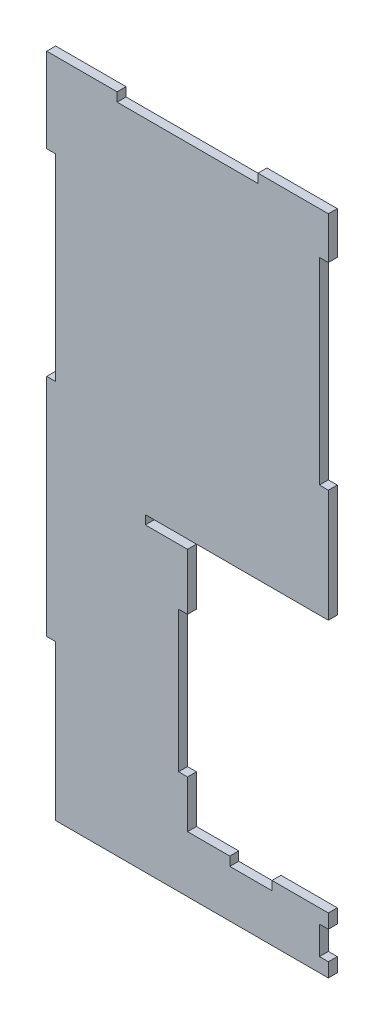
SolidWorks part; units mm, degrees
ref_plane "Front Plane" through (0, 0, 0) normal (0, 0, 1) x (1, 0, 0)
ref_plane "Top Plane" through (0, 0, 0) normal (0, 1, 0) x (1, 0, 0)
ref_plane "Right Plane" through (0, 0, 0) normal (1, 0, 0) x (0, 0, -1)
sketch "Sketch1" plane through (0, 0, 0) normal (0, 0, 1) x (1, 0, 0)
  line L0 (-186.7725, 0) -> (178.836, 0) construction
  line L1 (0, 287.0857) -> (0, -126.9841) construction
  line L2 (100, 287.0857) -> (100, -117.9894) construction
  line L3 (-179.3651, 235) -> (228.5714, 235) construction
  line L4 (-9.3722, 220) -> (110.0222, 220) construction
  line L5 (3.175, 0) -> (3.175, 55)
  line L6 (3.175, 55) -> (0, 55)
  line L7 (0, 55) -> (0, 135)
  line L8 (0, 135) -> (3.175, 135)
  line L9 (3.175, 135) -> (3.175, 205)
  line L10 (3.175, 205) -> (0, 205)
  line L11 (0, 205) -> (0, 235)
  line L12 (0, 235) -> (100, 235)
  line L13 (100, 235) -> (100, 220)
  line L14 (100, 110) -> (50, 110)
  line L15 (50, 106.825) -> (50, 86.825)
  line L16 (50, 20) -> (100, 20)
  line L17 (100, 20) -> (100, 0)
  line L18 (100, 0) -> (3.175, 0)
  line L19 (100, 220) -> (96.825, 220)
  line L20 (96.825, 220) -> (96.825, 150)
  line L21 (96.825, 150) -> (100, 150)
  line L22 (100, 150) -> (100, 110)
  line L23 (50, 110) -> (35, 110)
  line L24 (35, 110) -> (35, 106.825)
  line L25 (35, 106.825) -> (50, 106.825)
  line L26 (72.7222, 86.825) -> (-38.8167, 86.825) construction
  line L27 (50, 86.825) -> (46.825, 86.825)
  line L28 (46.825, 86.825) -> (46.825, 36.825)
  line L29 (46.825, 36.825) -> (50, 36.825)
  line L30 (50, 36.825) -> (50, 20)
  line L32 (46.825, 20) -> (115.3757, 20) construction
  dimension "D1" = 100
  dimension "D2" = 235
  dimension "D3" = 3.175
  dimension "D4" = 55
  dimension "D5" = 80
  dimension "D6" = 3.175
  dimension "D7" = 70
  dimension "D8" = 125
  dimension "D9" = 50
  dimension "D10" = 90
  dimension "D11" = 30
  dimension "D12" = 3.175
  dimension "D13" = 70
  dimension "D14" = 15
  dimension "D15" = 3.175
  dimension "D16" = 86.825
  dimension "D17" = 20
  dimension "D18" = 3.175
  dimension "D19" = 50
extrude "Boss-Extrude1" add sketch "Sketch1" against normal blind 3.175
ref_plane "Plane1" through (0, 0, 0) normal (0, 0, 1) x (1, 0, 0)
sketch "Sketch2" plane through (0, 0, 0) normal (0, 0, 1) x (1, 0, 0)
  line L0 (0, 0) -> (103.4598, 0) construction
  line L1 (0, 0) -> (0, 52.7996) construction
  line L2 (65, 34.2584) -> (65, -5.3954) construction
  line L3 (65, 20) -> (65, 16.825)
  line L4 (100, 20) -> (50, 20) construction
  line L5 (65, 16.825) -> (80, 16.825)
  line L6 (80, 16.825) -> (80, 20)
  line L7 (80, 20) -> (65, 20)
  dimension "D1" = 65
  dimension "D2" = 3.175
  dimension "D3" = 15
extrude "Cut-Extrude1" cut sketch "Sketch2" against normal blind 10
ref_plane "Plane2" through (0, 0, 0) normal (0, 0, 1) x (1, 0, 0)
sketch "Sketch3" plane through (0, 0, 0) normal (0, 0, 1) x (1, 0, 0)
  line L0 (25, 239.5402) -> (25, 199.3132) construction
  line L1 (0, 235) -> (0, 205) construction
  line L2 (25, 235) -> (25, 231.825)
  line L3 (100, 235) -> (0, 235) construction
  line L4 (25, 231.825) -> (75, 231.825)
  line L5 (75, 231.825) -> (75, 235)
  line L6 (75, 235) -> (25, 235)
  dimension "D1" = 25
  dimension "D2" = 3.175
  dimension "D3" = 50
extrude "Cut-Extrude2" cut sketch "Sketch3" against normal blind 10
ref_plane "Plane3" through (0, 0, 0) normal (0, 0, 1) x (1, 0, 0)
sketch "Sketch4" plane through (0, 0, 0) normal (0, 0, 1) x (1, 0, 0)
  line L0 (-3.7946, 0) -> (120.5672, 0) construction
  line L1 (0, 20) -> (116.6775, 20) construction
  line L2 (60.998, 15) -> (116.6775, 15) construction
  line L3 (62.1094, 5) -> (116.6775, 5) construction
  line L4 (96.825, 28.2171) -> (96.825, -11.5698) construction
  line L5 (100, 0) -> (100, 20) construction
  line L6 (100, 15) -> (96.825, 15)
  line L7 (96.825, 15) -> (96.825, 5)
  line L8 (96.825, 5) -> (100, 5)
  line L9 (100, 5) -> (100, 15)
  dimension "D1" = 20
  dimension "D2" = 5
  dimension "D3" = 5
  dimension "D4" = 3.175
extrude "Cut-Extrude3" cut sketch "Sketch4" against normal blind 10
